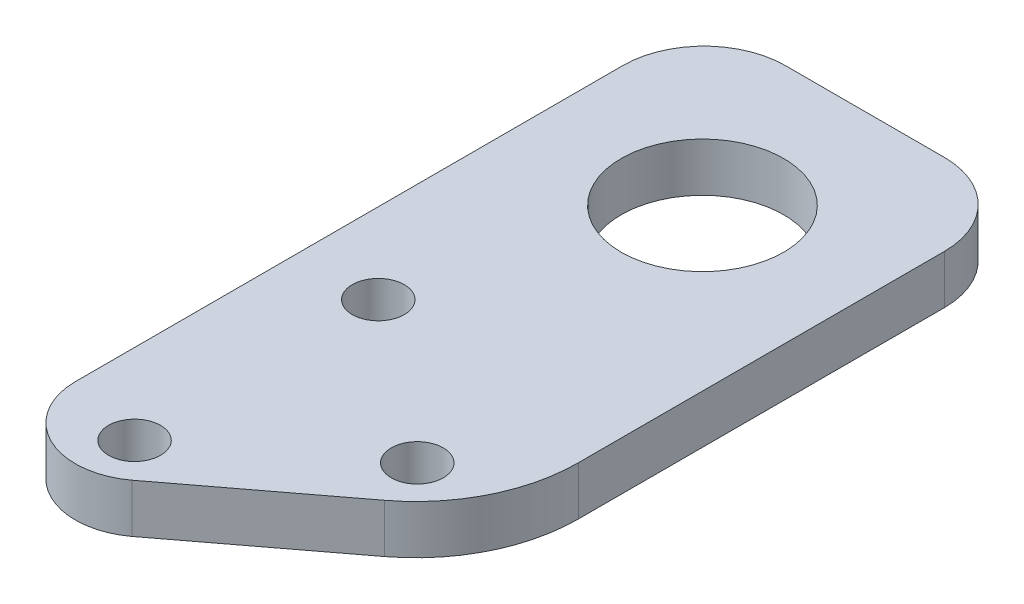
SolidWorks part; units mm, degrees
ref_plane "Front Plane" through (0, 0, 0) normal (0, 0, 1) x (1, 0, 0)
ref_plane "Top Plane" through (0, 0, 0) normal (0, 1, 0) x (1, 0, 0)
ref_plane "Right Plane" through (0, 0, 0) normal (1, 0, 0) x (0, 0, -1)
sketch "Sketch1" plane through (0, 0, 0) normal (0, 1, 0) x (1, 0, 0)
  line L5 (-9.9, 27.5) -> (-9.9, -6.1922)
  line L6 (-2.906, -9.7015) -> (5.9386, -3.0011)
  line L19 (9.9, 27.5) -> (9.9, 4.9698)
  line L20 (4.9, 32.5) -> (-4.9, 32.5)
  circle A0 centre (-4.95, 7.5) radius 1.6
  circle A1 centre (-4.95, -7.5) radius 1.6
  circle A2 centre (4.95, 0) radius 1.6
  arc A3 (-9.9, -6.1922) -> (-2.906, -9.7015) centre (-5.5226, -6.1922) ccw
  arc A5 (9.9, 4.9698) -> (5.9386, -3.0011) centre (-0.1, 4.9698) cw
  circle A6 centre (0, 22.5) radius 5
  arc A7 (-9.9, 27.5) -> (-4.9, 32.5) centre (-4.9, 27.5) cw
  arc A8 (9.9, 27.5) -> (4.9, 32.5) centre (4.9, 27.5) ccw
  point P0 (0, 0)
  point P2 (-9.9, -6.1922)
  point P23 (8.2713, -1.2339)
  dimension "D1" = 3.2
  dimension "D2" = 3.2
  dimension "D3" = 3.2
  dimension "D4" = 10
  dimension "D5" = 10
  dimension "D6" = 5
  dimension "D7" = 5
extrude "Boss-Extrude1" add sketch "Sketch1" along normal blind 3
